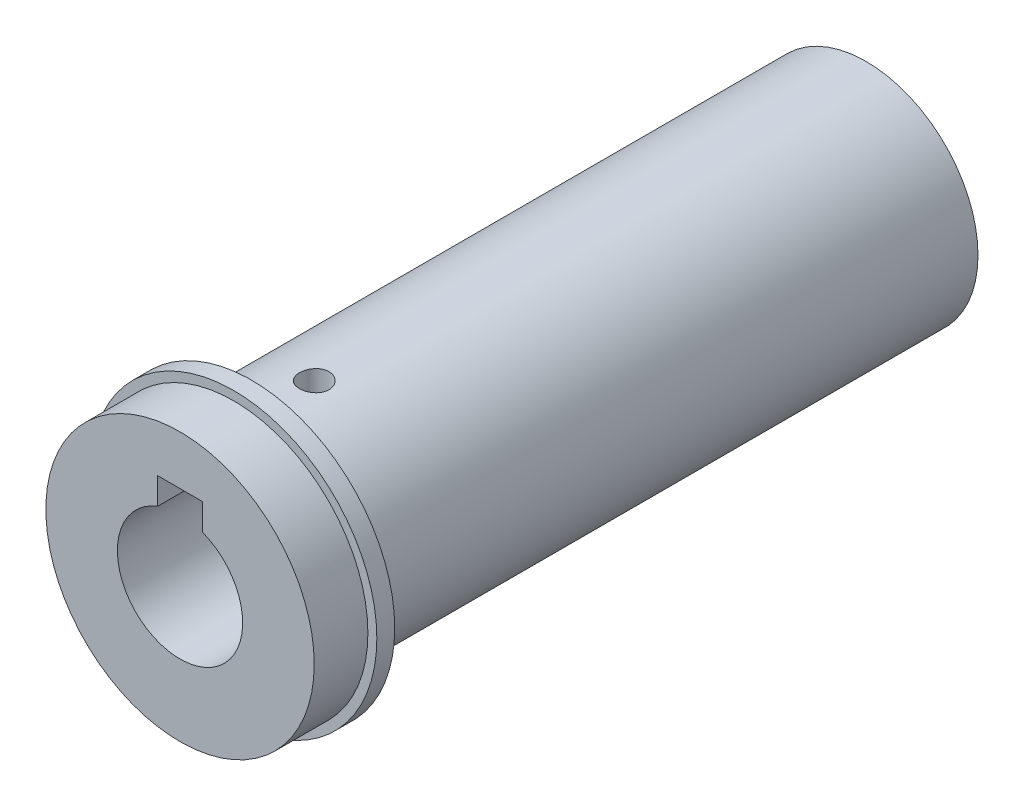
SolidWorks part; units mm, degrees
ref_plane "Front Plane" through (0, 0, 0) normal (0, 0, 1) x (1, 0, 0)
ref_plane "Top Plane" through (0, 0, 0) normal (0, 1, 0) x (1, 0, 0)
ref_plane "Right Plane" through (0, 0, 0) normal (1, 0, 0) x (0, 0, -1)
sketch "Sketch1" plane through (0, 0, 0) normal (0, 0, 1) x (1, 0, 0)
  circle A0 centre (0, 0) radius 12.5
  dimension "D1" = 25
extrude "Boss-Extrude1" add sketch "Sketch1" along normal blind 68.7
sketch "Sketch2" plane through (0, 0, 68.7) normal (0, 0, 1) x (1, 0, 0)
  circle A0 centre (0, 0) radius 16
  dimension "D1" = 32
extrude "Boss-Extrude2" add sketch "Sketch2" along normal blind 2
sketch "Sketch3" plane through (0, 0, 70.7) normal (0, 0, 1) x (1, 0, 0)
  circle A0 centre (0, 0) radius 15
  dimension "D1" = 30
extrude "Boss-Extrude3" add sketch "Sketch3" along normal blind 6
sketch "Sketch4" plane through (0, 0, 76.7) normal (0, 0, 1) x (1, 0, 0)
  line L1 (-2.5, 4.5) -> (2.5, 4.5)
  line L2 (-2.5, 4.5) -> (-2.5, 9.5)
  line L3 (-2.5, 9.5) -> (2.5, 9.5)
  line L4 (2.5, 4.5) -> (2.5, 9.5)
  line L5 (-2.5, 4.5) -> (2.5, 9.5) construction
  line L6 (-2.5, 9.5) -> (2.5, 4.5) construction
  circle A0 centre (0, 0) radius 7
  point P3 (0, 7)
  dimension "D1" = 14
  dimension "D2" = 5
  dimension "D3" = 5
extrude "Cut-Extrude1" cut sketch "Sketch4" against normal blind 30 contours L2 A0 L4 L1 | L4 A0 L2 L1 | A0 L4 L3 L2
ref_plane "Plane1" through (0, 0, 64.7) normal (0, 0, -1) x (-1, 0, 0)
sketch "Sketch6" plane through (0, 0, 64.7) normal (0, 0, -1) x (-1, 0, 0)
  line L0 (0, 55) -> (0, -55) construction
  line L1 (-3, -9.5) -> (3, -9.5)
  line L2 (-3, -9.5) -> (-3, -15.5)
  line L3 (-3, -15.5) -> (3, -15.5)
  line L4 (3, -9.5) -> (3, -15.5)
  line L5 (-3, -9.5) -> (3, -15.5) construction
  line L6 (-3, -15.5) -> (3, -9.5) construction
  circle A0 centre (0, 0) radius 12.5 construction
  point P0 (0, -12.5)
  dimension "D1" = 6
  dimension "D2" = 6
extrude "Cut-Extrude2" cut sketch "Sketch6" along normal blind 35
ref_plane "Plane2" through (0, 12.5, 0) normal (0, 1, 0) x (1, 0, 0)
hole_wizard "M4x0.7 Tapped Hole1" positions "Sketch8" profile "Sketch9" tap size "M4x0.7" standard "ANSI Metric" end condition up to next
sketch "Sketch8" plane through (0, 12.5, 0) normal (0, 1, 0) x (1, 0, 0)
  line L0 (0, -17.6) -> (0, 17.6) construction
  line L2 (-15, -76.7) -> (15, -76.7) construction
  point P0 (0, -61.7)
  dimension "D1" = 15
sketch "Sketch9" plane through (0, 12.5, 61.7) normal (1, 0, 0) x (0, 0, 1)
  line L0 (0, 0) -> (0, 3)
  line L1 (0, 3) -> (1.65, 3)
  line L2 (1.65, 3) -> (1.65, 0)
  line L5 (1.65, 0) -> (0, 0)
  line L11 (0, -6.35) -> (0, 107.95) construction
  dimension "Thread Major Dia." = 3.3
  dimension "Thru Tap Drill Depth" = 3
